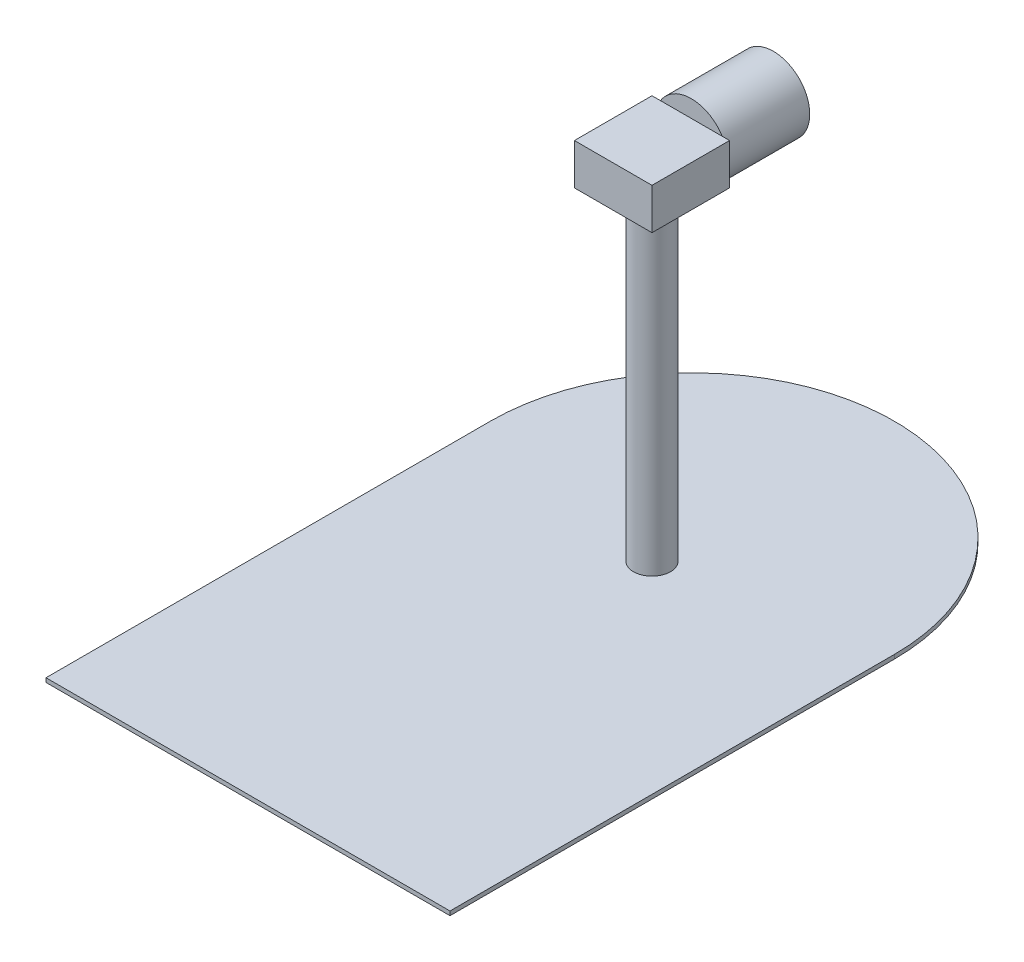
SolidWorks part; units mm, degrees
material "Teak"
ref_plane "Front Plane" through (0, 0, 0) normal (0, 0, 1) x (1, 0, 0)
ref_plane "Top Plane" through (0, 0, 0) normal (0, 1, 0) x (1, 0, 0)
ref_plane "Right Plane" through (0, 0, 0) normal (1, 0, 0) x (0, 0, -1)
sketch "Sketch1" plane through (0, 0, 0) normal (0, 1, 0) x (1, 0, 0)
  line L1 (132.6713, -150.4798) -> (-117.3287, -150.4798)
  line L2 (132.6713, -150.4798) -> (132.6713, 124.5202)
  line L4 (-117.3287, -150.4798) -> (-117.3287, 124.5202)
  arc A0 (132.6713, 124.5202) -> (-117.3287, 124.5202) centre (7.6713, 124.5202) ccw
  dimension "D3" = 250
  dimension "D2" = 250
extrude "Boss-Extrude1" add sketch "Sketch1" along normal blind 2.54
sketch "Sketch2" plane through (0, 2.54, 0) normal (0, 1, 0) x (1, 0, 0)
  circle A0 centre (7.6713, 99.5202) radius 11.4395
  arc A1 (132.6713, 124.5202) -> (-117.3287, 124.5202) centre (7.6713, 124.5202) ccw construction
  point P2 (7.6713, 249.5202)
  dimension "D1" = 150
extrude "Boss-Extrude2" add sketch "Sketch2" along normal blind 200
sketch "Sketch3" plane through (0, 202.54, 0) normal (0, 1, 0) x (1, 0, 0)
  line L0 (31.6713, 123.5202) -> (-16.3287, 75.5202) construction
  line L1 (31.6713, 75.5202) -> (-16.3287, 75.5202)
  line L2 (31.6713, 75.5202) -> (31.6713, 123.5202)
  line L3 (31.6713, 123.5202) -> (-16.3287, 123.5202)
  line L4 (-16.3287, 75.5202) -> (-16.3287, 123.5202)
  circle A0 centre (7.6713, 99.5202) radius 11.4395 construction
  circle A1 centre (7.6713, 99.5202) radius 11.4395
  circle M1 centre (7.6713, 99.5202) radius 11.4395
  dimension "D2" = 48
  dimension "D1" = 48
extrude "Boss-Extrude3" add sketch "Sketch3" along normal blind 25.4 contours L4 L1 M1 | L2 L3 M1 | L1 L2 M1 | L4 L1 M1 | L4 L3 M1
sketch "Sketch4" plane through (0, 0, -123.5202) normal (0, 0, -1) x (-1, 0, 0)
  circle A0 centre (-8.0008, 216.0514) radius 22.5
  dimension "D1" = 45
extrude "Boss-Extrude4" add sketch "Sketch4" along normal blind 50.8
